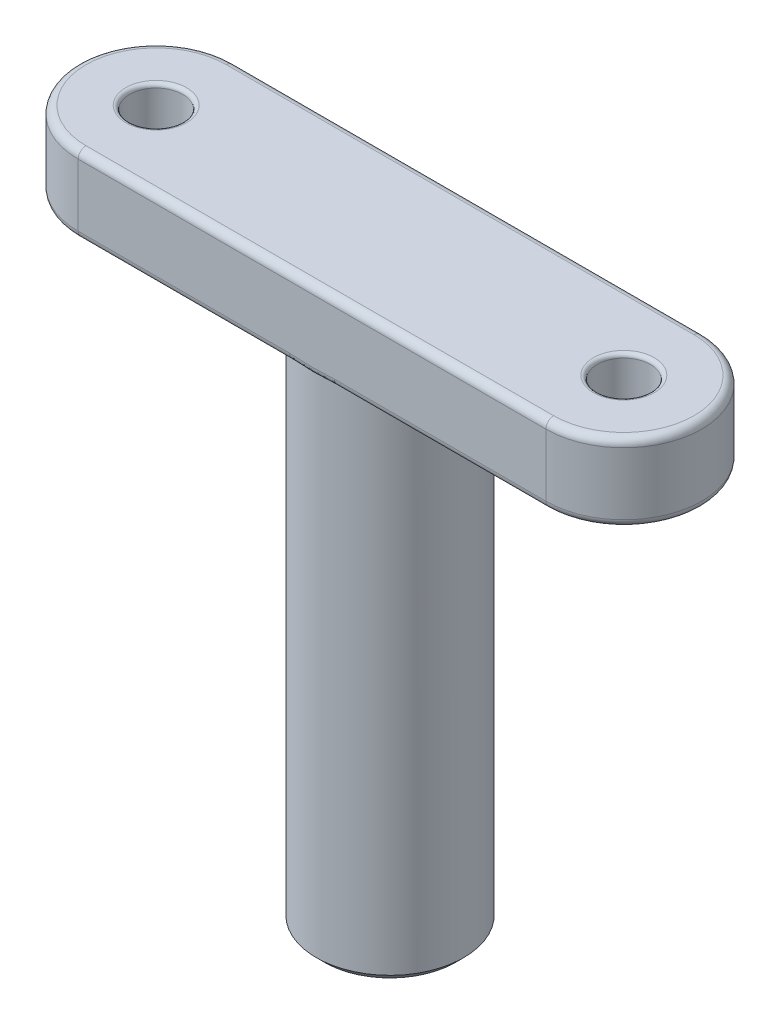
SolidWorks part; units mm, degrees
ref_plane "Front Plane" through (0, 0, 0) normal (0, 0, 1) x (1, 0, 0)
ref_plane "Top Plane" through (0, 0, 0) normal (0, 1, 0) x (1, 0, 0)
ref_plane "Right Plane" through (0, 0, 0) normal (1, 0, 0) x (0, 0, -1)
sketch "Sketch1" plane through (0, 0, 0) normal (0, 1, 0) x (1, 0, 0)
  line L0 (-15, 0) -> (15, 0) construction
  line L1 (-15, 5) -> (15, 5)
  line L2 (-15, -5) -> (15, -5)
  arc A0 (-15, 5) -> (-15, -5) centre (-15, 0) ccw
  arc A1 (15, -5) -> (15, 5) centre (15, 0) ccw
  point P3 (0, 0)
  dimension "D1" = 30
  dimension "D2" = 10
extrude "Boss-Extrude1" add sketch "Sketch1" along normal blind 5
hole_wizard "M3 Clearance Hole1" positions "Sketch2" profile "Sketch3" hole size "M3" standard "ANSI Metric"
sketch "Sketch2" plane through (0, 5, 0) normal (0, 1, 0) x (1, 0, 0)
  line L0 (15, 0) -> (-15, 0) construction
  point P0 (-15, 0)
  point P2 (15, 0)
  point P9 (0, 0)
  dimension "D1" = 30
sketch "Sketch3" plane through (-15, 5, 0) normal (1, 0, 0) x (0, 0, 1)
  line L0 (0, 0) -> (0, 6.0215)
  line L1 (0, 6.0215) -> (1.7, 5)
  line L2 (1.7, 5) -> (1.7, 0)
  line L5 (1.7, 0) -> (0, 0)
  line L10 (0, 6.0215) -> (-1.7, 5) construction
  line L11 (0, -6.35) -> (0, 107.95) construction
  dimension "Hole Dia." = 3.4
  dimension "Hole Depth" = 5
  dimension "Drill Angle" = 118
sketch "Sketch4" plane through (0, 0, 0) normal (0, -1, 0) x (1, 0, 0)
  circle A0 centre (0, 0) radius 4.725
  dimension "D1" = 9.45
extrude "Boss-Extrude2" add sketch "Sketch4" along normal blind 33
sketch "Sketch5" plane through (0, -33, 0) normal (0, -1, 0) x (1, 0, 0)
  circle A0 centre (0, 0) radius 3.025
  dimension "D1" = 6.05
extrude "Cut-Extrude1" cut sketch "Sketch5" against normal blind 2
fillet "Fillet1" radius 0.5 8 edges at (20, 5, 0) (0, 5, 5) (-20, 5, 0) (20, 0, 0) (0, 0, 5) (-20, 0, 0) (0, 5, -5) (0, 0, -5)
chamfer "Chamfer1" distance 0.5 angle 45 1 edges at (0, -33, -4.725)
fillet "Fillet2" radius 0.25 2 edges at (-15, 5, 1.7) (15, 5, 1.7)
